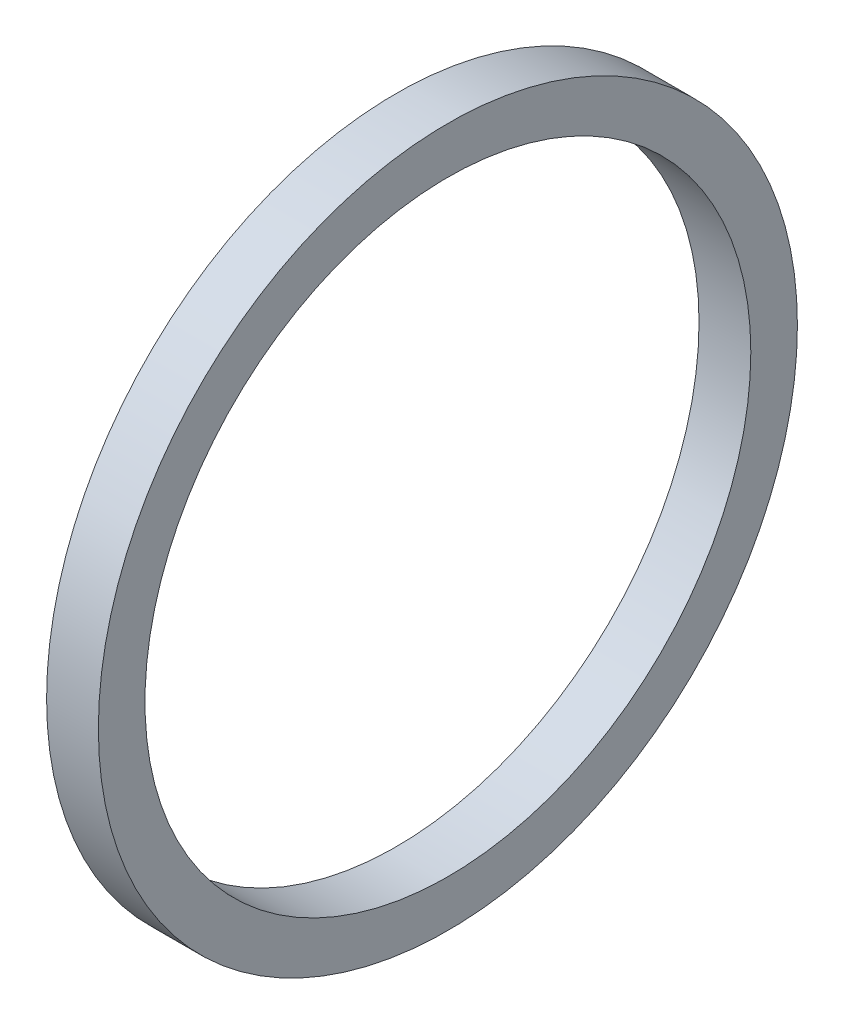
SolidWorks part; units mm, degrees
ref_plane "Front Plane" through (0, 0, 0) normal (0, 0, 1) x (1, 0, 0)
ref_plane "Top Plane" through (0, 0, 0) normal (0, 1, 0) x (1, 0, 0)
ref_plane "Right Plane" through (0, 0, 0) normal (1, 0, 0) x (0, 0, -1)
sketch "Sketch1" plane through (0, 0, 0) normal (1, 0, 0) x (0, 0, -1)
  circle A0 centre (-1.4776, 0.1567) radius 1.4859
  circle A1 centre (-1.4776, 0.1567) radius 1.7145
  dimension "D1" = 2.9718
  dimension "D2" = 3.429
extrude "Snap ring" add sketch "Sketch1" along normal blind 0.254
equation "\"D2@Sketch1\" = \"D1@Sketch1\"+.018"
